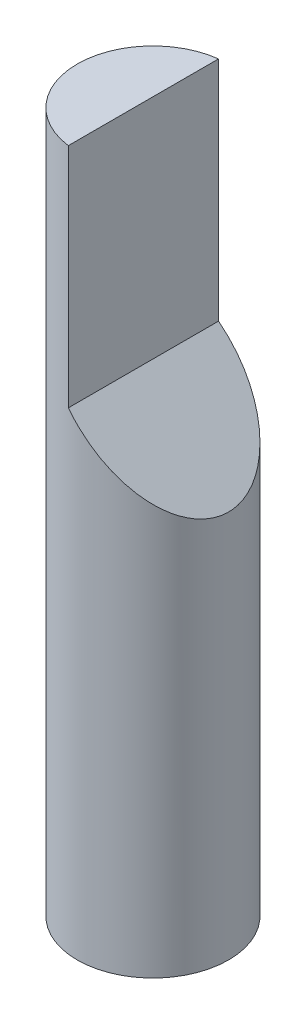
SolidWorks part; units mm, degrees
ref_plane "Front Plane" through (0, 0, 0) normal (0, 0, 1) x (1, 0, 0)
ref_plane "Top Plane" through (0, 0, 0) normal (0, 1, 0) x (1, 0, 0)
ref_plane "Right Plane" through (0, 0, 0) normal (1, 0, 0) x (0, 0, -1)
sketch "Sketch1" plane through (0, 0, 0) normal (0, 1, 0) x (1, 0, 0)
  circle A0 centre (0, 0) radius 0.4
  dimension "D1" = 0.8
extrude "Boss-Extrude1" add sketch "Sketch1" along normal blind 3.7
sketch "Sketch3" plane through (0, 0, 0) normal (0, 0, 1) x (1, 0, 0)
  line L0 (-0.05, 3.7) -> (-0.05, 2.5)
  line L1 (0.4, 3.7) -> (-0.4, 3.7) construction
  line L2 (-0.05, 2.5) -> (0.4, 2.05)
  line L3 (0, 0) -> (0, 3.7) construction
  line L4 (-0.4, 3.7) -> (-0.4, 0) construction
  line L5 (0.4, 3.7) -> (-0.05, 3.7)
  line L6 (0.4, 0) -> (0.4, 3.7) construction
  line L7 (0.4, 2.05) -> (0.4, 3.7)
  dimension "D1" = 45
  dimension "D2" = 1.2
  dimension "D3" = 0.35
extrude "Cut-Extrude1" cut sketch "Sketch3" against normal through all both and the other way through all
